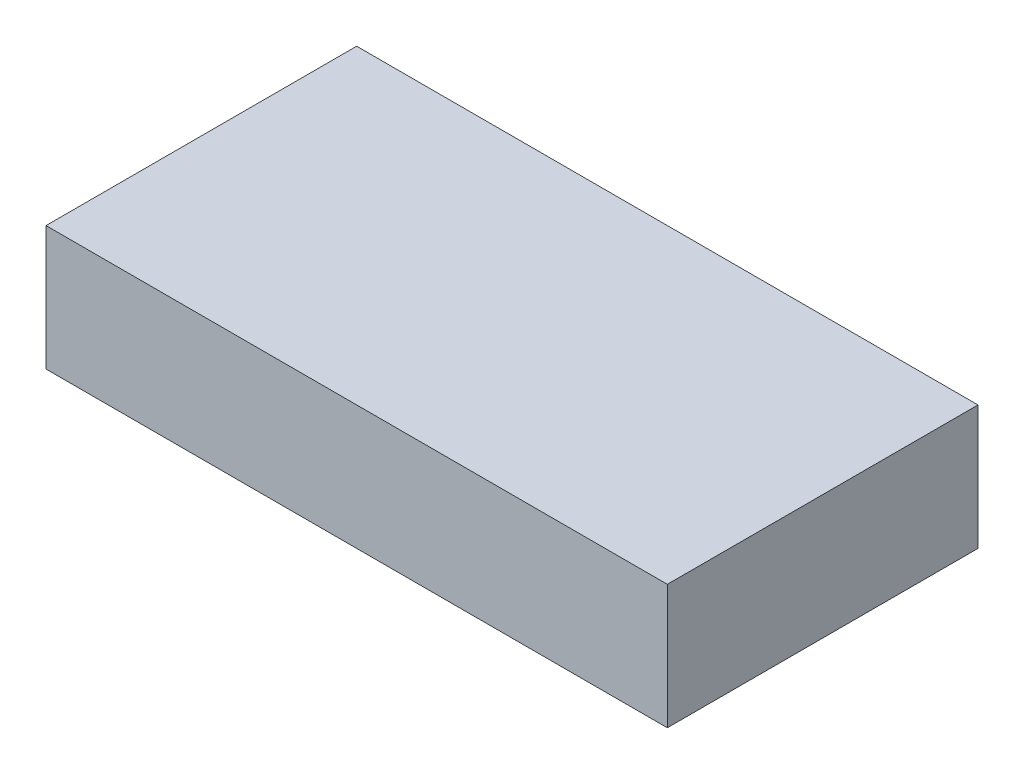
SolidWorks part; units mm, degrees
ref_plane "Front Plane" through (0, 0, 0) normal (0, 0, 1) x (1, 0, 0)
ref_plane "Top Plane" through (0, 0, 0) normal (0, 1, 0) x (1, 0, 0)
ref_plane "Right Plane" through (0, 0, 0) normal (1, 0, 0) x (0, 0, -1)
sketch "Sketch1" plane through (0, 0, 0) normal (0, 1, 0) x (1, 0, 0)
  line L1 (-64.9121, -29.1306) -> (135.0879, -29.1306)
  line L2 (-64.9121, -29.1306) -> (-64.9121, 70.8694)
  line L3 (-64.9121, 70.8694) -> (135.0879, 70.8694)
  line L4 (135.0879, -29.1306) -> (135.0879, 70.8694)
  dimension "D1" = 100
  dimension "D2" = 200
extrude "Boss-Extrude1" add sketch "Sketch1" along normal blind 40
